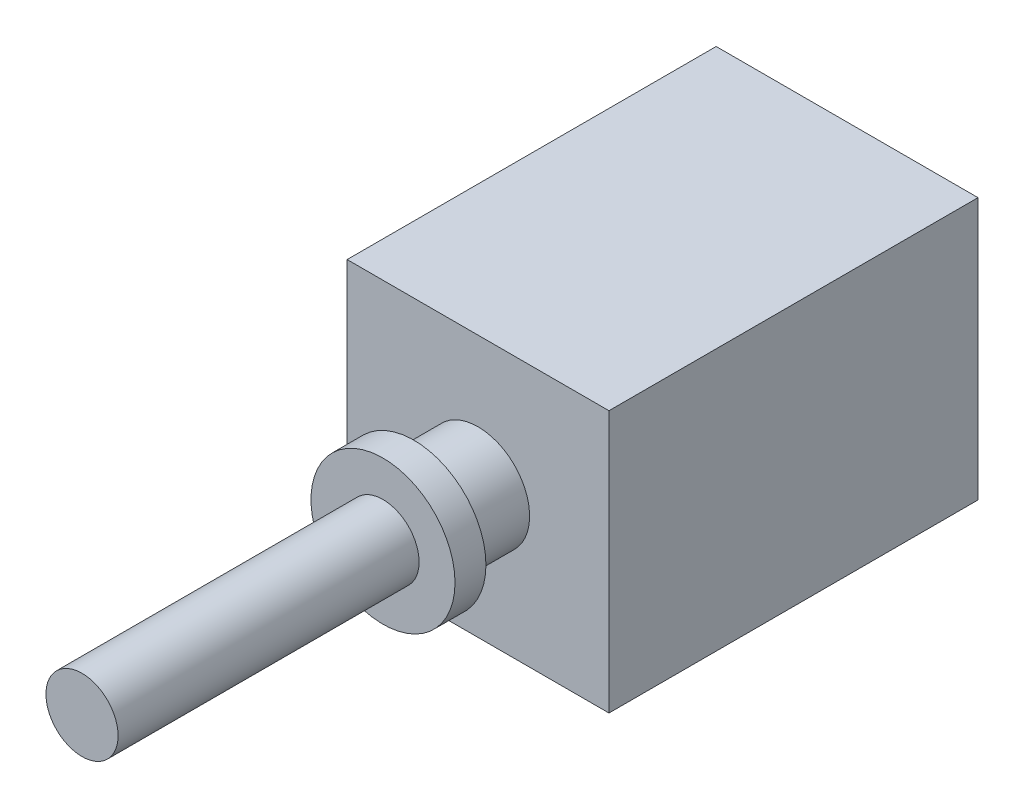
SolidWorks part; units mm, degrees
ref_plane "Front Plane" through (0, 0, 0) normal (0, 0, 1) x (1, 0, 0)
ref_plane "Top Plane" through (0, 0, 0) normal (0, 1, 0) x (1, 0, 0)
ref_plane "Right Plane" through (0, 0, 0) normal (1, 0, 0) x (0, 0, -1)
sketch "Sketch1" plane through (0, 0, 0) normal (0, 0, 1) x (1, 0, 0)
  line L0 (0, 33.085) -> (0, -29.1411) construction
  line L1 (30.9295, 0) -> (-32.068, 0) construction
  line L3 (-63.5, -63.5) -> (63.5, -63.5)
  line L4 (-63.5, -63.5) -> (-63.5, 63.5)
  line L5 (-63.5, 63.5) -> (63.5, 63.5)
  line L6 (63.5, -63.5) -> (63.5, 63.5)
  line L7 (-63.5, -63.5) -> (63.5, 63.5) construction
  line L8 (-63.5, 63.5) -> (63.5, -63.5) construction
  point P5 (0, 0)
  dimension "D1" = 127
  dimension "D2" = 127
extrude "Boss-Extrude1" add sketch "Sketch1" along normal blind 179
sketch "Sketch2" plane through (0, 0, 179) normal (0, 0, 1) x (1, 0, 0)
  circle A0 centre (0, 0) radius 25
  dimension "D1" = 50
extrude "Boss-Extrude2" add sketch "Sketch2" along normal blind 31.1
sketch "Sketch3" plane through (0, 0, 210.1) normal (0, 0, 1) x (1, 0, 0)
  circle A0 centre (0, 0) radius 34.925
  dimension "D1" = 69.85
extrude "Boss-Extrude3" add sketch "Sketch3" along normal blind 15
sketch "Sketch4" plane through (0, 0, 225.1) normal (0, 0, 1) x (1, 0, 0)
  circle A0 centre (0, 0) radius 17.5
  dimension "D1" = 35
extrude "Boss-Extrude4" add sketch "Sketch4" along normal blind 146
sketch "Sketch5" [suppressed] plane through (0, -63.5, 0) normal (0, -1, 0) x (1, 0, 0)
  line L0 (26.7138, 41.206) -> (26.7138, 176.5134) construction
  text T0 "RGA" font "Century Gothic" height in points 144
sketch "Sketch7" [suppressed] plane through (63.5, 0, 0) normal (1, 0, 0) x (0, 0, -1)
  text T0 "RGA" font "Century Gothic" height in points 144
sketch "Sketch8" [suppressed] plane through (0, 63.5, 0) normal (0, 1, 0) x (1, 0, 0)
  line L0 (11.6778, -139.4518) -> (11.6778, -4.1444) construction
  text T0 "RGA" font "Century Gothic" height in points 144
sketch "Sketch9" [suppressed] plane through (-63.5, 0, 0) normal (-1, 0, 0) x (0, 0, 1)
  line L0 (162.169, -49.2094) -> (162.169, 94.8033) construction
  line L1 (118.4746, 0) -> (51.7702, 0) construction
  text T0 "RGA" font "Century Gothic" height in points 144
